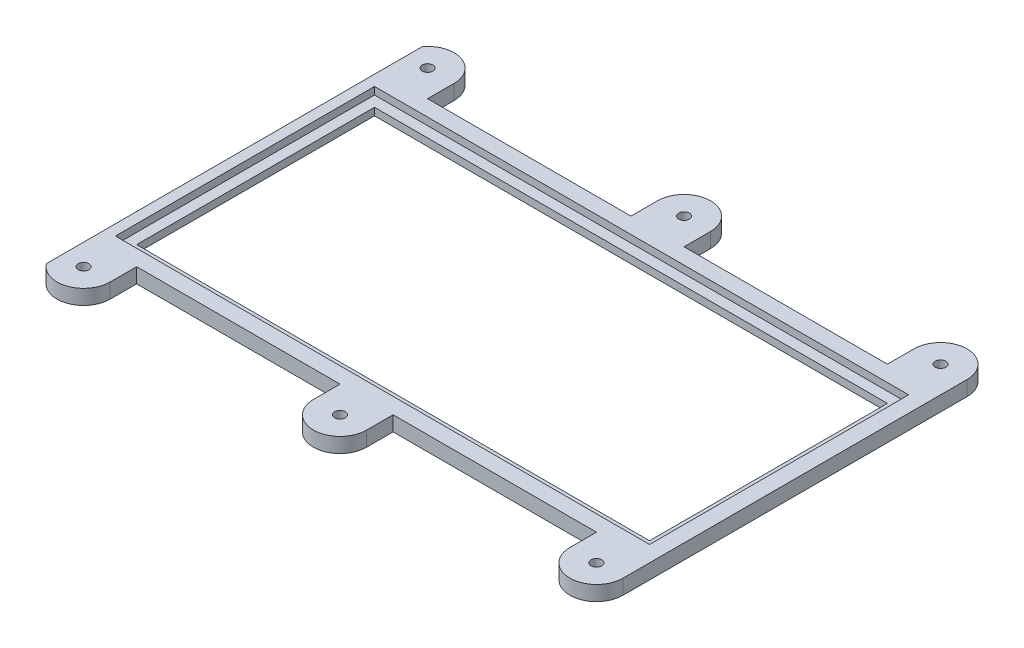
SolidWorks part; units mm, degrees
ref_plane "Front Plane" through (0, 0, 0) normal (0, 0, 1) x (1, 0, 0)
ref_plane "Top Plane" through (0, 0, 0) normal (0, 1, 0) x (1, 0, 0)
ref_plane "Right Plane" through (0, 0, 0) normal (1, 0, 0) x (0, 0, -1)
sketch "Sketch1" plane through (0, 0, 0) normal (0, 1, 0) x (1, 0, 0)
  line L9 (24.15, -11.2) -> (-24.15, -11.2)
  line L10 (24.15, -11.2) -> (24.15, 11.2)
  line L11 (24.15, 11.2) -> (-24.15, 11.2)
  line L16 (-24.15, -11.2) -> (-24.15, 11.2)
  line L18 (24.15, -11.2) -> (-24.15, 11.2) construction
  line L19 (24.15, 11.2) -> (-24.15, -11.2) construction
  line L20 (26.65, -13.7) -> (-26.65, -13.7)
  line L21 (26.65, -13.7) -> (26.65, 13.7)
  line L22 (26.65, 13.7) -> (-26.65, 13.7)
  line L23 (-26.65, -13.7) -> (-26.65, 13.7)
  line L24 (26.65, -13.7) -> (-26.65, 13.7) construction
  line L25 (26.65, 13.7) -> (-26.65, -13.7) construction
  point P0 (0, 0)
  point P5 (0, 0)
  dimension "D1" = 48.3
  dimension "D2" = 22.4
  dimension "D3" = 2.5
  dimension "D4" = 2.5
extrude "Boss-Extrude1" add sketch "Sketch1" along normal blind 0.7
sketch "Sketch2" plane through (0, 0.7, 0) normal (0, 1, 0) x (1, 0, 0)
  line L0 (-25.15, 12.2) -> (-25.15, -12.2)
  line L1 (-25.15, -12.2) -> (25.15, -12.2)
  line L2 (25.15, -12.2) -> (25.15, 12.2)
  line L3 (25.15, 12.2) -> (-25.15, 12.2)
  line L4 (-26.65, 13.7) -> (-26.65, -13.7)
  line L5 (-26.65, -13.7) -> (26.65, -13.7)
  line L6 (26.65, -13.7) -> (26.65, 13.7)
  line L7 (26.65, 13.7) -> (-26.65, 13.7)
  line L8 (-26.65, 13.7) -> (-26.65, -13.7)
  line L9 (-26.65, -13.7) -> (26.65, -13.7)
  line L10 (26.65, -13.7) -> (26.65, 13.7)
  line L11 (26.65, 13.7) -> (-26.65, 13.7)
  dimension "D1" = 0
  dimension "D2" = 1.5
extrude "Boss-Extrude2" add sketch "Sketch2" along normal blind 0.7
sketch "Sketch3" plane through (0, 0, 0) normal (0, -1, 0) x (1, 0, 0)
  line L5 (26.65, -13.7) -> (-26.65, -13.7) construction
  line L9 (-26.65, 13.7) -> (26.65, 13.7) construction
  line L26 (26.65, -13.7) -> (-26.65, -13.7)
  line L32 (-26.65, 13.7) -> (-21.65, 13.7)
  line L33 (-26.65, -13.7) -> (-26.65, 13.7) construction
  line L34 (26.65, 13.7) -> (26.65, -13.7) construction
  line L35 (-26.65, 13.7) -> (-26.65, 16.2)
  line L36 (-21.65, 16.2) -> (-21.65, 13.7)
  line L37 (26.65, 16.2) -> (26.65, 13.7)
  line L38 (21.65, 16.2) -> (21.65, 13.7)
  line L39 (2.5, 16.2) -> (2.5, 13.7)
  line L40 (-2.5, 16.2) -> (-2.5, 13.7)
  line L41 (-2.5, 13.7) -> (2.5, 13.7)
  line L42 (21.65, 13.7) -> (26.65, 13.7)
  arc A6 (-21.65, 16.2) -> (-26.65, 16.2) centre (-24.15, 16.2) ccw
  arc A7 (2.5, 16.2) -> (-2.5, 16.2) centre (0, 16.2) ccw
  arc A8 (26.65, 16.2) -> (21.65, 16.2) centre (24.15, 16.2) ccw
  circle A9 centre (-24.15, 16.2) radius 0.5
  circle A10 centre (0, 16.2) radius 0.5
  circle A11 centre (24.15, 16.2) radius 0.5
  dimension "D1" = 5
  dimension "D2" = 1
extrude "Boss-Extrude3" add sketch "Sketch3" against normal up to surface (1.4 mm away)
mirror "Mirror1" about plane through (0, 0, 0) normal (0, 0, 1) of "Boss-Extrude3"
sketch "Sketch5" plane through (0, 1.4, 0) normal (0, 1, 0) x (1, 0, 0)
  line L1 (-39.6977, 26.9384) -> (-26.15, 26.9384)
  line L2 (-39.6977, 26.9384) -> (-39.6977, -21.0173)
  line L3 (-39.6977, -21.0173) -> (-26.15, -21.0173)
  line L4 (-26.15, 26.9384) -> (-26.15, -21.0173)
  line L5 (-25.15, 12.2) -> (-25.15, -12.2) construction
  dimension "D1" = 1
extrude "Cut-Extrude1" cut sketch "Sketch5" against normal through all both and the other way through all
